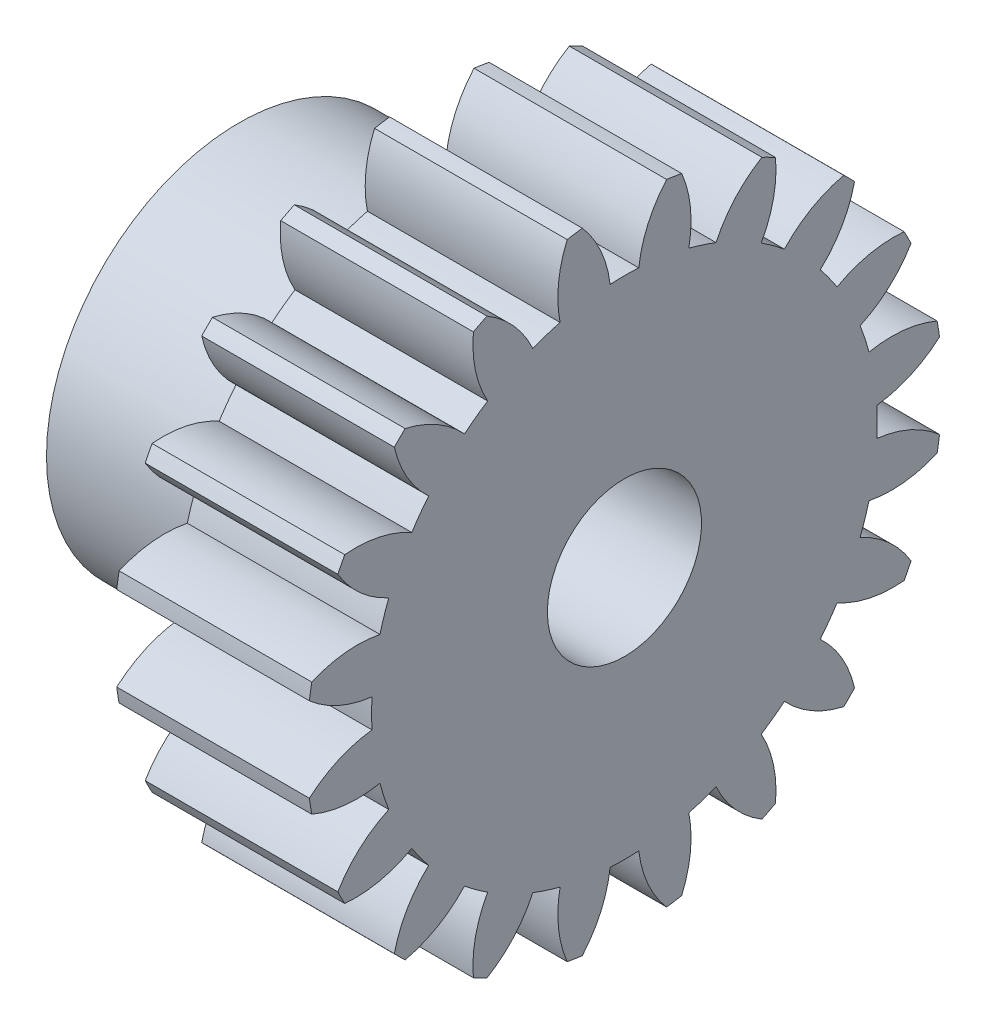
SolidWorks part; units mm, degrees
ref_plane "Plane1" through (0, 0, 0) normal (0, 0, 1) x (1, 0, 0)
ref_plane "Plane2" through (0, 0, 0) normal (0, 1, 0) x (1, 0, 0)
ref_plane "Plane3" through (0, 0, 0) normal (1, 0, 0) x (0, 0, -1)
other "Configuration Table"
sketch "HoldingSke" plane through (0, 0, 0) normal (0, 1, 0) x (1, 0, 0)
  line L0 (0, 0) -> (0.6265, -0.228)
  line L1 (-15, 0) -> (100, 0) construction
  line L2 (0, 0) -> (-2.1039, 2.3779)
  line L3 (0, 0) -> (-11.863, 4.5341)
  line L4 (0, 0) -> (8.1152, 2.9537)
  line L5 (0, 0) -> (-18.7391, -6.9891)
  line L6 (0, 0) -> (-8.2896, -5.593)
  line L7 (-2.1039, 2.3779) -> (2.2011, 21.9091)
  line L8 (-76.2, 54.61) -> (-74.8, 54.61)
  line L9 (-71.009, 38.7566) -> (-53.1078, 45.2721)
  line L10 (-76.2, 71.12) -> (104.1128, 71.12)
  line L11 (0, 0) -> (-10, 0)
  line L12 (-76.2, 101.6) -> (-76.147, 101.6)
  line L13 (24.9733, 27.94) -> (52.9518, 28.4284)
  line L14 (24.9733, 27.94) -> (24.9743, 27.94)
  line L15 (24.9733, 27.94) -> (100.4006, 29.5858)
  line L16 (-63.627, -1.5) -> (-12.827, -1.5)
  circle A0 centre (0, 0) radius 4
  circle A1 centre (0, 0) radius 10
  circle A2 centre (0, 0) radius 10
  circle A3 centre (0, 0) radius 4
  dimension "MHD" = 20
  dimension "Hub_dia" = 20
  dimension "Bore" = 8
  dimension "MBD" = 8
  dimension "Num_teeth" = 20
  dimension "Pitch" = 0.6667
  dimension "Overall_len" = 20
  dimension "Show_teeth" = 20
  dimension "Thickness" = 10
  dimension "OAL" = 20.0001
  dimension "T_dim" = 1.4
  dimension "Ap" = 20
  dimension "H" = 19.05
  dimension "Pitch_radius" = 180.3128
  dimension "Width" = 10
  dimension "Backlash" = 0.053
  dimension "Addendum_fac" = 1
  dimension "Dedendum_fac" = 1.25
  dimension "Clearance_fac" = 0.25
  dimension "Dedendum_add" = 0.001
  dimension "Module" = 1.5
sketch "BasProSke" plane through (0, 0, 0) normal (0, 1, 0) x (1, 0, 0)
  line L0 (-10, 0) -> (60, 0) construction
  line L1 (0, 0) -> (0, 16.5)
  line L2 (0, 0) -> (10, 0)
  line L3 (10, 0) -> (10, 16.5)
  line L4 (10, 16.5) -> (0, 16.5)
  dimension "Thickness" = 10
  dimension "Diameter" = 33
revolve "Base-Revolve" add sketch "BasProSke" angle 360 about L0
sketch "TooCutSke" plane through (0, 0, 0) normal (1, 0, 0) x (0, 0, -1)
  line L1 (0, 0) -> (0, 107) construction
  line L2 (0, 0) -> (-1.2696, 14.9462) construction
  line L3 (0, 0) -> (-4.6808, 29.5532) construction
  line L4 (-1.2696, 14.9462) -> (-2.3404, 14.7766) construction
  arc A0 (0.7438, 13.1029) -> (-0.7438, 13.1029) centre (0, 0) ccw
  arc A1 (2.21, 16.377) -> (-2.21, 16.377) centre (0, 0) ccw
  circle A2 centre (0, 0) radius 15 construction
  circle A3 centre (0, 0) radius 14.0954 construction
  arc A4 (-0.7438, 13.1029) -> (-2.21, 16.377) centre (-6.7025, 12.3999) ccw
  arc A5 (2.21, 16.377) -> (0.7438, 13.1029) centre (6.7025, 12.3999) ccw
  dimension "Root_dia" = 26.248
  dimension "Overcut_dia" = 33.0508
  dimension "Pitch_dia" = 30
  dimension "Base_dia" = 28.1908
  dimension "Flank_rad" = 6
  dimension "Half_ang" = 9
  dimension "Half_CT" = 1.0841
extrude "ToothCut" cut sketch "TooCutSke" along normal through all
fillet "Breaks" [suppressed] radius 0.03
fillet "RootFillets" [suppressed] radius 0.376
pattern_circular "TeethCuts" count 20 every 18 about axis through (-10, 0, 0) along (1, 0, 0) of "ToothCut", "RootFillets", "Breaks"
sketch "HubNeaOneSke" plane through (0, 0, 0) normal (-1, 0, 0) x (0, 0, 1)
  circle A0 centre (0, 0) radius 10
  dimension "Diameter" = 20
extrude "HubNearOne" add sketch "HubNeaOneSke" along normal blind 10.0001
sketch "HubNeaBotSke" plane through (0, 0, 0) normal (-1, 0, 0) x (0, 0, 1)
  circle A0 centre (0, 0) radius 10
  dimension "Diameter" = 20
extrude "HubNearBoth" [suppressed] add sketch "HubNeaBotSke" along normal blind 5
ref_plane "FarPln" through (10, 0, 0) normal (1, 0, 0) x (0, 0, -1)
sketch "HubFarSke" plane through (10, 0, 0) normal (1, 0, 0) x (0, 0, -1)
  circle A0 centre (0, 0) radius 10
  dimension "Diameter" = 20
extrude "HubFar" [suppressed] add sketch "HubFarSke" along normal blind 5
sketch "BorSke" plane through (0, 0, 0) normal (1, 0, 0) x (0, 0, -1)
  circle A0 centre (0, 0) radius 4
  dimension "Diameter" = 8
extrude "Bore" cut sketch "BorSke" along normal mid plane 40.0001
sketch "KeySke" plane through (0, 0, 0) normal (1, 0, 0) x (0, 0, -1)
  line L0 (-1.5, 0) -> (-1.5, 5.4)
  line L1 (-1.5, 5.4) -> (1.5, 5.4)
  line L2 (1.5, 5.4) -> (1.5, 0)
  line L3 (0, 0) -> (0, 34) construction
  line L4 (-1.5, 0) -> (1.5, 0)
  dimension "Offset" = 5.4
  dimension "Width" = 3
extrude "Keyway" [suppressed] cut sketch "KeySke" along normal mid plane 40.0001
pattern_circular "Keyway2" [suppressed] count 2 every 90 about axis through (-10, 0, 0) along (1, 0, 0)
sketch "Sketch2" plane through (-10.0001, 0, 0) normal (-1, 0, 0) x (0, 0, 1)
  line L0 (3.1248, -2) -> (7.445, -2)
  line L1 (3.1248, 2) -> (7.445, 2)
  line L2 (-3.1248, -2) -> (-7.445, -2)
  line L3 (-3.1248, 2) -> (-7.445, 2)
  arc A0 (7.445, -2) -> (7.445, 2) centre (7.445, 0) ccw
  arc A1 (-7.445, 2) -> (-7.445, -2) centre (-7.445, 0) ccw
  arc A2 (3.1248, 2) -> (-3.1248, 2) centre (0, 0) ccw
  arc A3 (-3.1248, -2) -> (3.1248, -2) centre (0, 0) ccw
extrude "Cut-Extrude1" cut sketch "Sketch2" against normal blind 5
equation "' \"Module@HoldingSke\" = 6.35"
equation "' \"Num_teeth@HoldingSke\" = 12"
equation "' \"Ap@HoldingSke\" =  20"
equation "' \"Ap@HoldingSke\" = 20"
equation "' \"Width@HoldingSke\" = 0.5 * 25.4"
equation "' \"Hub_dia@HoldingSke\"= 1 * 25.4"
equation "' \"Hub_dia@HoldingSke\" = 1 * 25.4"
equation "' \"Overall_len@HoldingSke\" = 1.0 * 25.4"
equation "' \"Bore@HoldingSke\" = 0.75 * 25.4"
equation "' \"T_dim@HoldingSke\" = 0.1 * 25.4"
equation "' \"Width@KeySke\" = 0.25 * 25.4"
equation "' \"Show_teeth@HoldingSke\" = 13"
equation "' \"Backlash@HoldingSke\" = 0.009 * 25.4"
equation "' \"Addendum_fac@HoldingSke\" = 1.0"
equation "' \"Dedendum_fac@HoldingSke\" = 1.25"
equation "' \"Dedendum_add@HoldingSke\" = 0.00005 * 25.4"
equation "' \"Clearance_fac@HoldingSke\" = 0.25"
equation "\"Pitch@HoldingSke\" = 1 / \"Module@HoldingSke\""
equation "\"Overcut_dia@TooCutSke\" = (\"Num_teeth@HoldingSke\" + 2 * \"Addendum_fac@HoldingSke\") / \"Pitch@HoldingSke\" + 0.002 * 25.4"
equation "\"Pitch_dia@TooCutSke\" = \"Num_teeth@HoldingSke\" / \"Pitch@HoldingSke\""
equation "\"Base_dia@TooCutSke\" = \"Num_teeth@HoldingSke\" / \"Pitch@HoldingSke\" * cos((\"Ap@HoldingSke\"  * 3.14159265 / 180))"
equation "\"Root_dia@TooCutSke\" = (\"Num_teeth@HoldingSke\" + 2) / \"Pitch@HoldingSke\" - 2 * (\"Addendum_fac@HoldingSke\" + \"Dedendum_fac@HoldingSke\") / \"Pitch@HoldingSke\" - \"Dedendum_add@HoldingSke\" * 2"
equation "\"Half_ang@TooCutSke\" = 180 / \"Num_teeth@HoldingSke\""
equation "\"Half_CT@TooCutSke\" = \"Num_teeth@HoldingSke\" / \"Pitch@HoldingSke\" * sin((3.14159265 / 2 / \"Num_teeth@HoldingSke\")) / 2 - 7 * \"Backlash@HoldingSke\" / 4"
equation "\"Flank_rad@TooCutSke\" = \"Num_teeth@HoldingSke\" / \"Pitch@HoldingSke\" / 5"
equation "\"Radius@RootFillets\" = \"Clearance_fac@HoldingSke\" / \"Pitch@HoldingSke\" + \"Dedendum_add@HoldingSke\""
equation "\"Break_rad@Breaks\" = 0.02 / \"Pitch@HoldingSke\""
equation "\"Thickness@HoldingSke\" = \"Width@HoldingSke\""
equation "\"OAL@HoldingSke\" = \"Thickness@HoldingSke\""
equation "\"MHD@HoldingSke\" = (\"Num_teeth@HoldingSke\" + 2) / \"Pitch@HoldingSke\" - 2 * (\"Addendum_fac@HoldingSke\" + \"Dedendum_fac@HoldingSke\")  / \"Pitch@HoldingSke\" - \"Dedendum_add@HoldingSke\" * 2"
equation "\"MBD@HoldingSke\" = (\"Num_teeth@HoldingSke\" + 2) / \"Pitch@HoldingSke\" - 2 * (\"Addendum_fac@HoldingSke\" + \"Dedendum_fac@HoldingSke\")  / \"Pitch@HoldingSke\" - \"Dedendum_add@HoldingSke\" * 2 - 0.002 * 25.4"
equation "\"MHD@HoldingSke\" = ((sgn( \"MHD@HoldingSke\" - \"Hub_dia@HoldingSke\" )-1)*( \"MHD@HoldingSke\" - \"Hub_dia@HoldingSke\" ))/-2+ \"Hub_dia@HoldingSke\""
equation "\"MBD@HoldingSke\" = ((sgn( \"MBD@HoldingSke\" - \"Bore@HoldingSke\" )-1)*( \"MBD@HoldingSke\" - \"Bore@HoldingSke\" ))/-2+ \"Bore@HoldingSke\""
equation "\"OAL@HoldingSke\" = ((sgn( \"OAL@HoldingSke\" - \"Overall_len@HoldingSke\" )+1)*( \"OAL@HoldingSke\" - \"Overall_len@HoldingSke\" ))/2 + \"Overall_len@HoldingSke\" + 0.000002 * 25.4"
equation "\"Num_teeth@TeethCuts\" = int( \"Show_teeth@HoldingSke\" ) + 1"
equation "\"Num_teeth@TeethCuts\" = ((sgn( \"Num_teeth@TeethCuts\" - \"Num_teeth@HoldingSke\" )-1)*( \"Num_teeth@TeethCuts\" - \"Num_teeth@HoldingSke\" ))/-2+ \"Num_teeth@HoldingSke\""
equation "\"Num_teeth@TeethCuts\" = ((sgn( \"Num_teeth@TeethCuts\" - 2.0)+1)*( \"Num_teeth@TeethCuts\" - 2.0))/2 +2.0"
equation "\"Angle@TeethCuts\" = 360.0 / \"Num_teeth@HoldingSke\""
equation "\"Diameter@BasProSke\" = (\"Num_teeth@HoldingSke\" + 2 * \"Addendum_fac@HoldingSke\") / \"Pitch@HoldingSke\""
equation "\"Thickness@BasProSke\"  = \"Thickness@HoldingSke\""
equation "' \"Fillet_rad@BasProSke\" =  \"Thickness@HoldingSke\" * 0.05"
equation "' \"Fillet_rad@BasProSke\" = \"Thickness@HoldingSke\" * 0.05"
equation "\"MHD@HoldingSke\" = ((sgn( \"MHD@HoldingSke\" - \"Root_dia@TooCutSke\" )-1)*( \"MHD@HoldingSke\" - \"Root_dia@TooCutSke\" ))/-2+ \"Root_dia@TooCutSke\""
equation "\"Diameter@HubNeaOneSke\" = \"MHD@HoldingSke\""
equation "\"Length@HubNearOne\" = \"OAL@HoldingSke\" - \"Thickness@BasProSke\""
equation "\"Diameter@HubNeaBotSke\" = \"MHD@HoldingSke\""
equation "\"Length@HubNearBoth\" = ( \"OAL@HoldingSke\" - \"Thickness@BasProSke\" ) / 2.0"
equation "\"Thickness@FarPln\" = \"Thickness@BasProSke\""
equation "\"Diameter@HubFarSke\" = \"MHD@HoldingSke\""
equation "\"Length@HubFar\" = ( \"OAL@HoldingSke\" - \"Thickness@BasProSke\" ) / 2.0"
equation "\"Diameter@BorSke\" = \"MBD@HoldingSke\""
equation "\"D1@Bore\" = \"OAL@HoldingSke\" * 2.0"
equation "\"D1@Keyway\" = \"OAL@HoldingSke\" * 2.0"
equation "\"Offset@KeySke\" = \"T_dim@HoldingSke\" + \"MBD@HoldingSke\" / 2.0"
